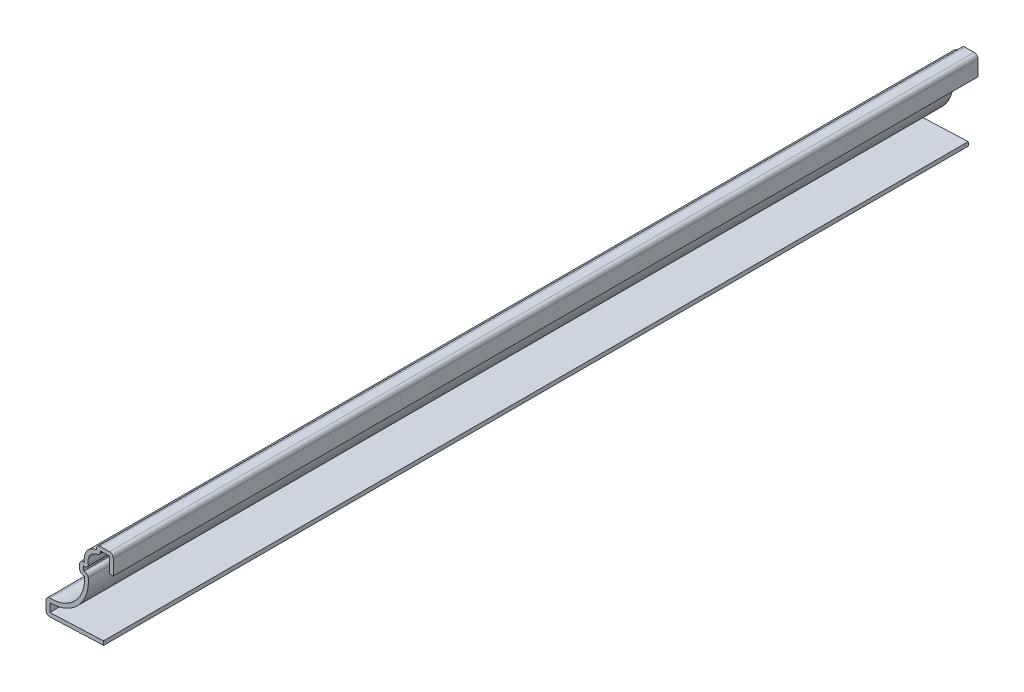
SolidWorks part; units mm, degrees
ref_plane "Front Plane" through (0, 0, 0) normal (0, 0, 1) x (1, 0, 0)
ref_plane "Top Plane" through (0, 0, 0) normal (0, 1, 0) x (1, 0, 0)
ref_plane "Right Plane" through (0, 0, 0) normal (1, 0, 0) x (0, 0, -1)
sketch "Sketch1" plane through (0, 0, 0) normal (0, 0, 1) x (1, 0, 0)
  line L0 (0, 0) -> (-19.05, -0.7937)
  line L1 (-19.05, -0.7937) -> (-19.05, 4.7625)
  line L2 (-6.35, 16.6688) -> (-7.9375, 16.6688)
  line L3 (-7.9375, 16.6688) -> (-7.9375, 20.6375)
  line L4 (-7.9375, 20.6375) -> (-6.35, 20.6375)
  line L5 (-2.3813, 26.1938) -> (-2.3813, 27.7812)
  line L6 (-2.3813, 27.7812) -> (3.175, 27.7812)
  line L7 (3.175, 27.7812) -> (3.175, 21.4313)
  arc A0 (-19.05, 4.7625) -> (-6.35, 16.6688) centre (-17.4249, 15.7555) ccw
  arc A1 (-6.35, 20.6375) -> (-2.3813, 26.1938) centre (-1.6636, 21.4856) cw
  point P11 (0, 0)
  point P15 (0, 0)
  point P16 (-2.3245, 26.0285)
  point P17 (0, 0)
  point P18 (0, 0)
  point P19 (0, 0)
  point P20 (0, 0)
  point P21 (-0.4883, 0.5306)
  dimension "D4" = 11.1125
  dimension "D11" = 4.7625
  dimension "D1" = 0.7937
  dimension "D2" = 19.05
  dimension "D3" = 5.5562
  dimension "D5" = 11.9062
  dimension "D6" = 1.5875
  dimension "D7" = 3.9688
  dimension "D8" = 1.5875
  dimension "D9" = 5.5562
  dimension "D10" = 3.9688
  dimension "D12" = 1.5875
  dimension "D13" = 5.5562
  dimension "D14" = 6.35
  dimension "D15" = 3.175
extrude "Extrude-Thin1" add sketch "Sketch1" against normal blind 285.75 thin
fillet "Fillet1" radius 1.27 9 edges at (3.175, 27.7812, -142.875) (-1.1113, 24.9342, -142.875) (-2.3813, 27.7812, -142.875) (-5.2364, 17.9388, -142.875) (-4.4405, 19.3675, -142.875) (-7.9375, 16.6688, -142.875) (-7.9375, 20.6375, -142.875) (-19.05, -0.7937, -142.875) (-19.05, 4.7625, -142.875)
